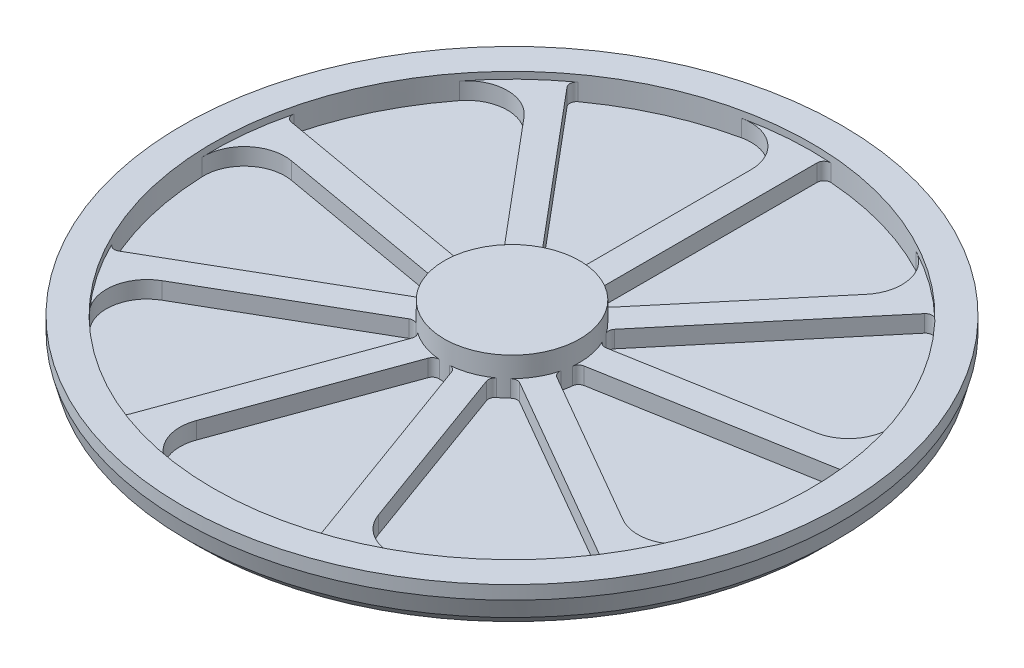
SolidWorks part; units mm, degrees
material "1060 Alloy"
ref_plane "Front Plane" through (0, 0, 0) normal (0, 0, 1) x (1, 0, 0)
ref_plane "Top Plane" through (0, 0, 0) normal (0, 1, 0) x (1, 0, 0)
ref_plane "Right Plane" through (0, 0, 0) normal (1, 0, 0) x (0, 0, -1)
sketch "Sketch1" plane through (0, 0, 0) normal (0, 1, 0) x (1, 0, 0)
  circle A0 centre (0, 0) radius 486.25
  dimension "D1" = 972.5
extrude "Boss-Extrude1" add sketch "Sketch1" along normal blind 65
sketch "Sketch3" plane through (0, 65, 0) normal (0, 1, 0) x (1, 0, 0)
  circle A0 centre (0, 0) radius 441.25
  dimension "D1" = 882.5
extrude "Cut-Extrude1" cut sketch "Sketch3" against normal offset from surface (35 mm away) 30 up to face at (0, 0, 486.25)
ref_axis "Axis1" through (0, 89.25, 0) along (0, -1, 0)
sketch "Sketch5" plane through (0, 0, 0) normal (1, 0, 0) x (0, 0, -1)
  line L0 (486.25, 65) -> (486.25, 45) construction
  line L1 (486.25, 0) -> (486.25, 65) construction
  line L2 (486.25, 45) -> (478.9295, 17.6795)
  line L3 (478.9295, 17.6795) -> (461.25, 0)
  line L4 (-486.25, 0) -> (486.25, 0) construction
  line L5 (461.25, 0) -> (486.25, 0)
  line L6 (486.25, 0) -> (486.25, 45)
  dimension "D1" = 20
  dimension "D2" = 15
  dimension "D3" = 45
  dimension "D4" = 25
revolve "Cut-Revolve1" cut sketch "Sketch5" angle 360 about axis through (0, 89.25, 0) along (0, -1, 0)
sketch "Sketch6" plane through (0, 30, 0) normal (0, 1, 0) x (1, 0, 0)
  circle A0 centre (0, 0) radius 100
  dimension "D1" = 200
extrude "Boss-Extrude3" add sketch "Sketch6" along normal blind 55
sketch "Sketch7" plane through (0, 30, 0) normal (0, 1, 0) x (1, 0, 0)
  line L0 (-20, 105.8301) -> (-20, 372.7621)
  line L1 (20, 430.2053) -> (20, 105.8301)
  line L2 (0, 0) -> (0, 745.6564)
  line L3 (30.6957, 440.181) -> (-15.3881, 461.1502)
  line L4 (-15.3881, 461.1502) -> (-92.5902, 431.4263)
  line L5 (27.2727, 96.2091) -> (7.6538, 82.3231)
  line L6 (7.6538, 82.3231) -> (-27.2727, 96.2091)
  arc A3 (-92.5902, 431.4263) -> (-20, 372.7621) centre (-80, 372.7621) cw
  arc A5 (30.6957, 440.181) -> (20, 430.2053) centre (30, 430.2053) ccw
  arc A6 (27.2727, 96.2091) -> (20, 105.8301) centre (30, 105.8301) cw
  arc A7 (-20, 105.8301) -> (-27.2727, 96.2091) centre (-30, 105.8301) cw
  circle M7 centre (0, 0) radius 100
  circle M8 centre (0, 0) radius 441.25
  dimension "D3" = 60
  dimension "D5" = 10
  dimension "D1" = 20
  dimension "40" = 40
extrude "Boss-Extrude4" add sketch "Sketch7" along normal offset from surface (25 mm away) 10 contours A6 L1 A5 L2 M7 M8 | L0 A7 L2 A3 M7 M8 up to face at (0, 65, 441.25)
pattern_circular "CirPattern1" count 9 over 360 about axis through (0, 0, 0) along (0, 1, 0) of "Boss-Extrude4"
equation "\"A\"= 65"
equation "\"B\"= 972.5"
equation "\"D1@Sketch1\"=\"B\""
equation "\"D1@Boss-Extrude1\"=\"A\""
equation "\"D1@Sketch3\"=\"B\"-90"
equation "\"D1@Boss-Extrude3\"=\"A\"+20-30"
